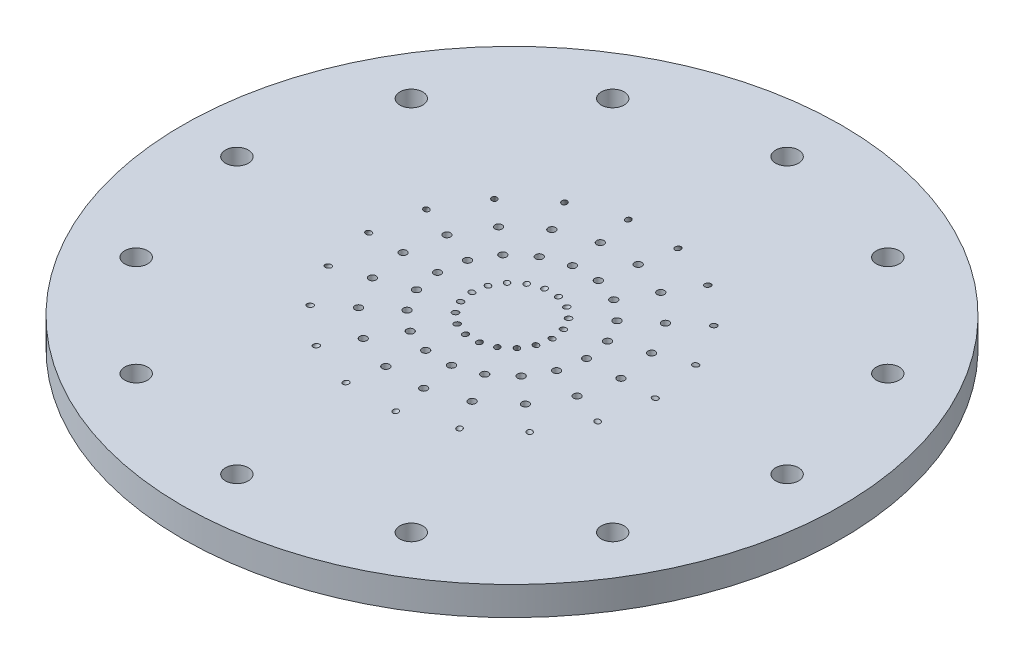
SolidWorks part; units mm, degrees
material "6061-T6 (SS)"
ref_plane "Front Plane" through (0, 0, 0) normal (0, 0, 1) x (1, 0, 0)
ref_plane "Top Plane" through (0, 0, 0) normal (0, 1, 0) x (1, 0, 0)
ref_plane "Right Plane" through (0, 0, 0) normal (1, 0, 0) x (0, 0, -1)
sketch "Sketch1" plane through (0, 0, 0) normal (0, 1, 0) x (1, 0, 0)
  circle A0 centre (0, 0) radius 73.025
  dimension "D1" = 146.05
extrude "Boss-Extrude1" add sketch "Sketch1" along normal blind 6.35 contours A0
sketch "Sketch2" plane through (0, 6.35, 0) normal (0, 1, 0) x (1, 0, 0)
  circle A0 centre (0, 0) radius 8.89
  circle A1 centre (0, 0) radius 16.51
  circle A2 centre (0, 0) radius 24.13
  circle A3 centre (0, 0) radius 31.75
  dimension "D1" = 17.78
  dimension "D2" = 33.02
  dimension "D3" = 48.26
  dimension "D4" = 63.5
sketch "Sketch3" plane through (0, 0, 0) normal (0, 0, 1) x (1, 0, 0)
  line L0 (8.89, 6.35) -> (0, -9.0479)
  line L1 (8.89, 6.35) -> (-8.89, 6.35) construction
  line L2 (16.51, 6.35) -> (-16.51, 6.35) construction
  line L3 (0, 0) -> (0, -9.0479) construction
  line L4 (0, -9.0479) -> (-8.5376, -4.1187) construction
  dimension "D1" = 30
ref_plane "Plane1" through (-3.9179, -6.7859, 0) normal (0.5, 0.866, 0) x (-0.866, 0.5, 0)
sketch "Sketch4" plane through (-3.9179, -6.7859, 0) normal (0.5, 0.866, 0) x (-0.866, 0.5, 0)
  line L0 (-4.524, 0) -> (5.3344, 0) construction
  circle A0 centre (-4.524, 0) radius 0.5906
  dimension "D1" = 1.1811
extrude "Cut-Extrude1" cut sketch "Sketch4" along normal through all
sketch "Sketch5" plane through (0, 0, 0) normal (0, 0, 1) x (1, 0, 0)
  line L0 (31.75, 6.35) -> (35.4162, 0)
  line L3 (31.75, 6.35) -> (-31.75, 6.35) construction
  line L4 (35.4162, 0) -> (0, 0) construction
  line L5 (31.75, 6.35) -> (52.6029, 18.3894) construction
  dimension "D1" = 60
ref_plane "Plane2" through (5.1879, -8.9857, 0) normal (0.5, -0.866, 0) x (0.866, 0.5, 0)
sketch "Sketch6" plane through (5.1879, -8.9857, 0) normal (0.5, -0.866, 0) x (0.866, 0.5, 0)
  circle A0 centre (30.6713, 0) radius 0.5906
  dimension "D1" = 1.1811
extrude "Cut-Extrude2" cut sketch "Sketch6" against normal through all both and the other way through all
sketch "Sketch7" plane through (0, 6.35, 0) normal (0, 1, 0) x (1, 0, 0)
  line L0 (0, 0) -> (31.75, 0) construction
  circle A0 centre (0, 0) radius 31.75 construction
  circle A1 centre (24.13, 0) radius 0.8065
  circle A2 centre (0, 0) radius 24.13 construction
  circle A3 centre (16.51, 0) radius 0.8065
  circle A7 centre (0, 0) radius 16.51 construction
  dimension "D1" = 1.6129
extrude "LOx Holes" cut sketch "Sketch7" against normal through all both and the other way through all
pattern_circular "CirPattern1" count 18 over 360 about axis through (0, 0, 0) along (0, 1, 0) of "Cut-Extrude1", "Cut-Extrude2", "LOx Holes"
sketch "Sketch8" plane through (0, 0, 0) normal (0, -1, 0) x (1, 0, 0)
  circle A0 centre (0, 0) radius 60.96 construction
  circle A1 centre (-60.96, 0) radius 2.54
  dimension "D1" = 121.92
  dimension "D2" = 5.08
extrude "Cut-Extrude4" cut sketch "Sketch8" against normal through all
pattern_circular "CirPattern2" count 12 over 360 about axis through (0, 0, 0) along (0, 1, 0) of "Cut-Extrude4"
